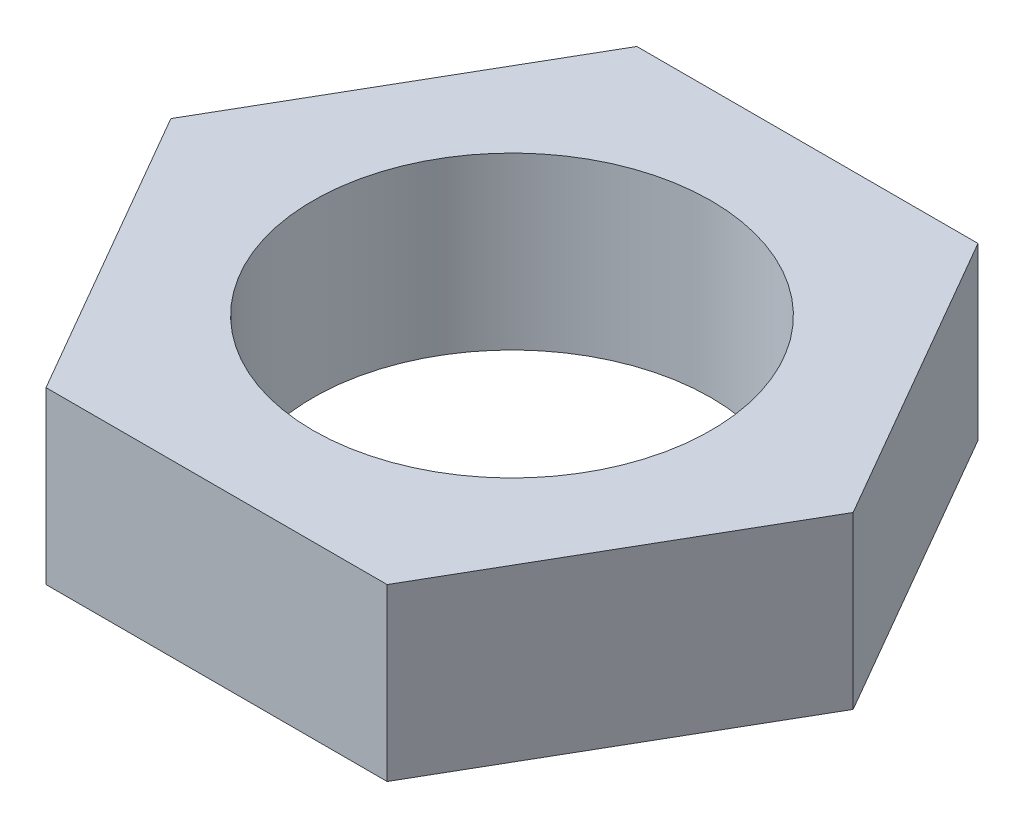
SolidWorks part; units mm, degrees
ref_plane "Front Plane" through (0, 0, 0) normal (0, 0, 1) x (1, 0, 0)
ref_plane "Top Plane" through (0, 0, 0) normal (0, 1, 0) x (1, 0, 0)
ref_plane "Right Plane" through (0, 0, 0) normal (1, 0, 0) x (0, 0, -1)
sketch "Sketch1" plane through (0, 0, 0) normal (0, 1, 0) x (1, 0, 0)
  line L1 (6, 0) -> (3, 5.1962)
  line L2 (3, 5.1962) -> (-3, 5.1962)
  line L3 (-3, 5.1962) -> (-6, 0)
  line L4 (-6, 0) -> (-3, -5.1962)
  line L5 (-3, -5.1962) -> (3, -5.1962)
  line L6 (3, -5.1962) -> (6, 0)
  circle A0 centre (0, 0) radius 5.1962 construction
  dimension "D1" = 6
extrude "Boss-Extrude1" add sketch "Sketch1" along normal blind 3
sketch "Sketch2" plane through (0, 3, 0) normal (0, 1, 0) x (1, 0, 0)
  circle A0 centre (0, 0) radius 3.5
  circle A1 centre (0, 0) radius 3.5 construction
extrude "Cut-Extrude1" cut sketch "Sketch2" against normal through all contours A0
